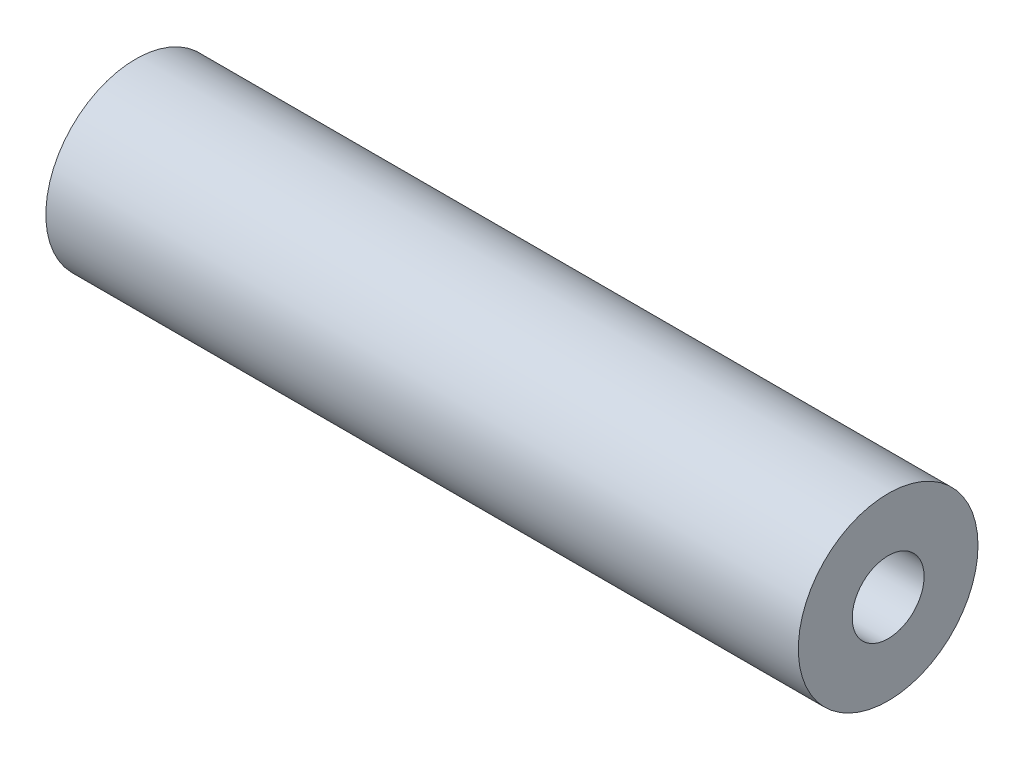
SolidWorks part; units mm, degrees
ref_plane "Alzado" through (0, 0, 0) normal (0, 0, 1) x (1, 0, 0)
ref_plane "Planta" through (0, 0, 0) normal (0, 1, 0) x (1, 0, 0)
ref_plane "Vista lateral" through (0, 0, 0) normal (1, 0, 0) x (0, 0, -1)
sketch "Croquis1" plane through (0, 0, 0) normal (1, 0, 0) x (0, 0, -1)
  circle A0 centre (0, 0) radius 8
  dimension "D1" = 16
extrude "Saliente-Extruir1" add sketch "Croquis1" along normal mid plane 67
hole_wizard "Taladro de margen para M61" positions "Croquis2" profile "Croquis4" hole size "M6" standard "ISO"
sketch "Croquis2" plane through (-33.5, 0, 0) normal (-1, 0, 0) x (0, 0, 1)
  point P0 (0, 0)
sketch "Croquis4" plane through (-33.5, 0, 0) normal (0, 1, 0) x (0, 0, 1)
  line L0 (0, 0) -> (0, 21.9228)
  line L1 (0, 21.9228) -> (3.2, 20)
  line L2 (3.2, 20) -> (3.2, 0)
  line L5 (3.2, 0) -> (0, 0)
  line L10 (0, 21.9228) -> (-3.2, 20) construction
  line L11 (0, -6.35) -> (0, 107.95) construction
  dimension "Diámetro de taladro" = 6.4
  dimension "Profundidad de taladro" = 20
  dimension "Ángulo de perforador" = 118
hole_wizard "Taladro de margen para M62" positions "Croquis5" profile "Croquis6" hole size "M6" standard "ISO"
sketch "Croquis5" plane through (33.5, 0, 0) normal (1, 0, 0) x (0, 0, -1)
  point P0 (0, 0)
sketch "Croquis6" plane through (33.5, 0, 0) normal (0, 1, 0) x (0, 0, -1)
  line L0 (0, 0) -> (0, 21.9228)
  line L1 (0, 21.9228) -> (3.2, 20)
  line L2 (3.2, 20) -> (3.2, 0)
  line L5 (3.2, 0) -> (0, 0)
  line L10 (0, 21.9228) -> (-3.2, 20) construction
  line L11 (0, -6.35) -> (0, 107.95) construction
  dimension "Diámetro de taladro" = 6.4
  dimension "Profundidad de taladro" = 20
  dimension "Ángulo de perforador" = 118
